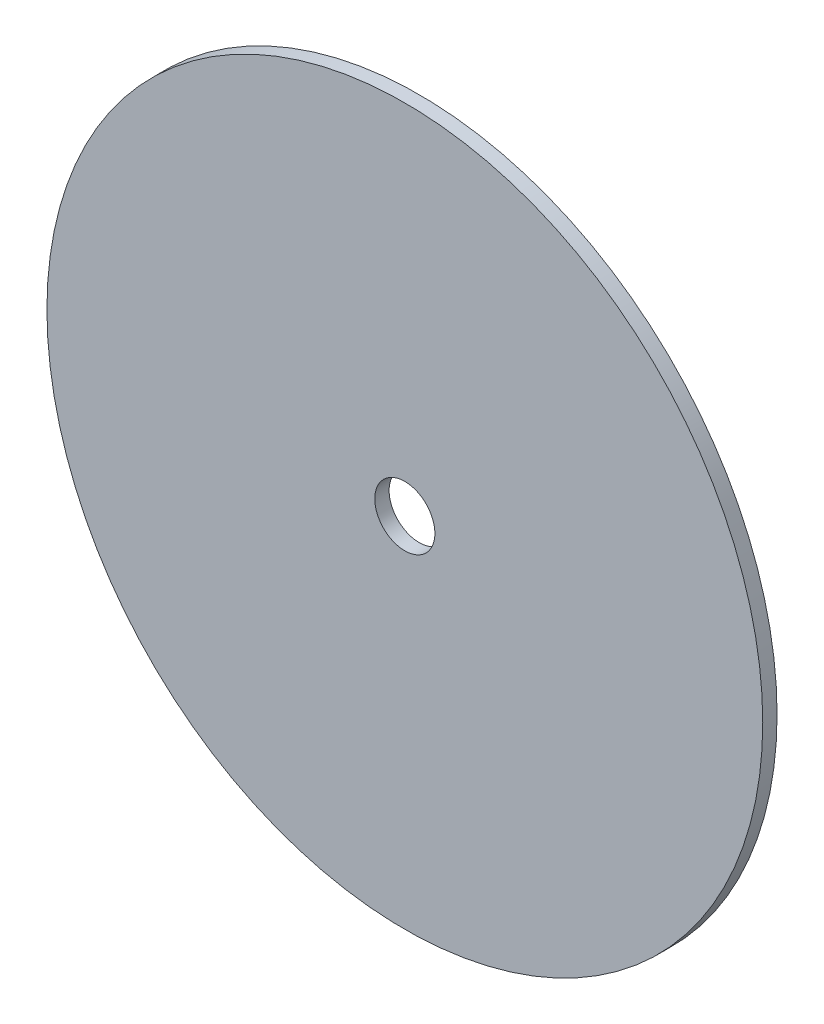
SolidWorks part; units mm, degrees
material "1.0038 (S235JRG2)"
ref_plane "Plan de face" through (0, 0, 0) normal (0, 0, 1) x (1, 0, 0)
ref_plane "Plan de dessus" through (0, 0, 0) normal (0, 1, 0) x (1, 0, 0)
ref_plane "Plan de droite" through (0, 0, 0) normal (1, 0, 0) x (0, 0, -1)
sketch "Esquisse1" plane through (0, 0, 0) normal (0, 0, 1) x (1, 0, 0)
  circle A0 centre (0, 0) radius 150
  circle A1 centre (0, 0) radius 12.6
  dimension "D1" = 25.2
  dimension "D2" = 300
extrude "Boss.-Extru.1" add sketch "Esquisse1" along normal blind 6
